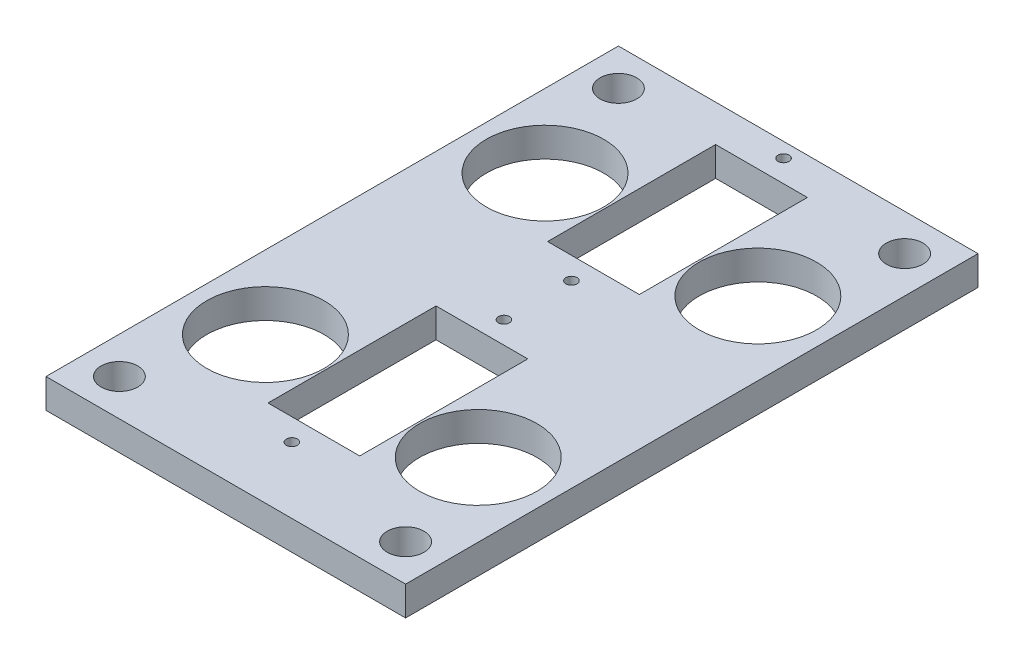
SolidWorks part; units mm, degrees
ref_plane "Alzado" through (0, 0, 0) normal (0, 0, 1) x (1, 0, 0)
ref_plane "Planta" through (0, 0, 0) normal (0, 1, 0) x (1, 0, 0)
ref_plane "Vista lateral" through (0, 0, 0) normal (1, 0, 0) x (0, 0, -1)
sketch "Croquis1" plane through (0, 0, 0) normal (0, 1, 0) x (1, 0, 0)
  line L0 (0, 37) -> (0, 32) construction
  line L1 (-24.5, 37) -> (24.5, 37)
  line L2 (-24.5, 37) -> (-24.5, -36)
  line L3 (-24.5, -36) -> (24.5, -36)
  line L4 (24.5, 37) -> (24.5, -36)
  line L5 (0, -29) -> (0, -36) construction
  line L6 (-6.25, -6.1) -> (-24.5, -6.1) construction
  line L7 (-14.5, -21.1) -> (14.5, -21.1) construction
  line L8 (-6.25, -6.1) -> (6.25, -6.1)
  line L9 (-6.25, -6.1) -> (-6.25, -29)
  line L10 (-6.25, -29) -> (6.25, -29)
  line L11 (6.25, -6.1) -> (6.25, -29)
  line L14 (6.25, 32) -> (-6.25, 32)
  line L15 (6.25, 32) -> (6.25, 9.1)
  line L16 (6.25, 9.1) -> (-6.25, 9.1)
  line L17 (-6.25, 32) -> (-6.25, 9.1)
  circle A0 centre (14.5, -21.1) radius 8
  circle A1 centre (-14.5, -21.1) radius 8
  circle A2 centre (-14.5, 17) radius 8
  circle A3 centre (14.5, 17) radius 8
  circle A6 centre (-19.5, 32) radius 2.5
  circle A7 centre (19.5, 32) radius 2.5
  point P0 (0, 0)
  point P10 (0, -17.55)
  dimension "D1" = 12.5
  dimension "D8" = 14.9
  dimension "D16" = 16
  dimension "D17" = 16
  dimension "D18" = 10
  dimension "D10" = 20
  dimension "D11" = 20
  dimension "D13" = 10
  dimension "D14" = 16
  dimension "D15" = 16
  dimension "D9" = 10
  dimension "D19" = 10
  dimension "D30" = 5
  dimension "D31" = 5
  dimension "D32" = 5
  dimension "D33" = 5
  dimension "D34" = 5
  dimension "D35" = 5
  dimension "D2" = 12.5
  dimension "D3" = 22.9
  dimension "D4" = 5
  dimension "D5" = 22.9
  dimension "D6" = 7
  dimension "D12" = 49
  dimension "D20" = 73
  dimension "D21" = 15.2
  dimension "D22" = 15
  dimension "D23" = 7.9
extrude "Saliente-Extruir4" add sketch "Croquis1" along normal blind 4
sketch "Croquis5" plane through (0, 4, 0) normal (0, 1, 0) x (1, 0, 0)
  line L0 (0, -6.1) -> (0, -3.1) construction
  line L1 (6.25, -6.1) -> (-6.25, -6.1) construction
  line L2 (0, 9.1) -> (0, 6.1) construction
  line L3 (-6.25, 9.1) -> (6.25, 9.1) construction
  line L4 (0, -29) -> (0, -32) construction
  line L5 (-6.25, -29) -> (6.25, -29) construction
  line L6 (0, 32) -> (0, 35) construction
  line L7 (6.25, 32) -> (-6.25, 32) construction
  circle A0 centre (0, 35) radius 0.75
  circle A1 centre (0, 6.1) radius 0.75
  circle A2 centre (0, -3.1) radius 0.75
  circle A3 centre (0, -32) radius 0.75
  dimension "D5" = 1.5
  dimension "D6" = 1.5
  dimension "D7" = 1.5
  dimension "D8" = 1.5
  dimension "D1" = 3
  dimension "D2" = 3
  dimension "D3" = 3
  dimension "D4" = 3
extrude "Cortar-Extruir1" cut sketch "Croquis5" against normal blind 4
sketch "Croquis7" plane through (0, 4, 0) normal (0, 1, 0) x (1, 0, 0)
  line L1 (-24.5, -36) -> (24.5, -36)
  line L2 (-24.5, -36) -> (-24.5, -41)
  line L3 (-24.5, -41) -> (24.5, -41)
  line L4 (24.5, -36) -> (24.5, -41)
  dimension "D1" = 49
  dimension "D2" = 5
extrude "Saliente-Extruir5" add sketch "Croquis7" against normal up to surface (4 mm away) up to face at (0, 0, -34.25)
sketch "Croquis8" plane through (0, 4, 0) normal (0, 1, 0) x (1, 0, 0)
  line L0 (-19.5, -36) -> (19.5, -36) construction
  line L1 (-24.5, -41) -> (24.5, -41) construction
  line L2 (24.5, -41) -> (24.5, 37) construction
  line L3 (-24.5, 37) -> (-24.5, -41) construction
  circle A0 centre (-19.5, -36) radius 2.5
  circle A1 centre (19.5, -36) radius 2.5
  dimension "D2" = 5
  dimension "D3" = 5
  dimension "D4" = 5
  dimension "D5" = 5
  dimension "D1" = 5
extrude "Cortar-Extruir2" cut sketch "Croquis8" against normal blind 10
